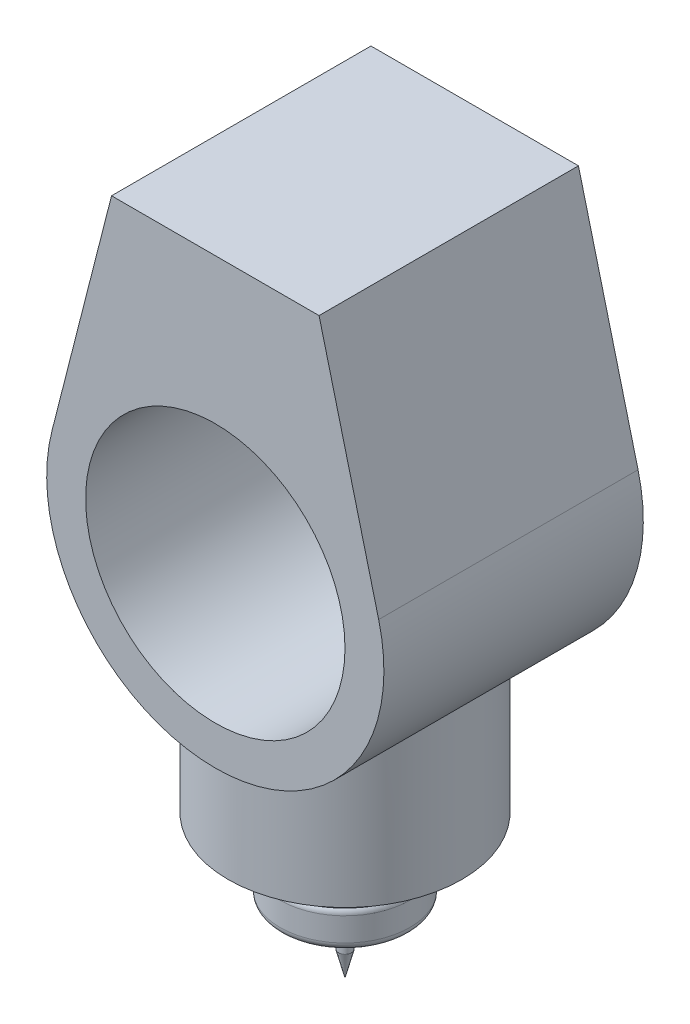
SolidWorks part; units mm, degrees
ref_plane "Front Plane" through (0, 0, 0) normal (0, 0, 1) x (1, 0, 0)
ref_plane "Top Plane" through (0, 0, 0) normal (0, 1, 0) x (1, 0, 0)
ref_plane "Right Plane" through (0, 0, 0) normal (1, 0, 0) x (0, 0, -1)
sketch "Sketch1" plane through (0, 0, 0) normal (0, 0, 1) x (1, 0, 0)
  line L0 (0, -45.712) -> (0, 32.0347) construction
  line L1 (0, 15.2605) -> (-20, 15.2605)
  line L2 (-20, 15.2605) -> (-20, 1.2605)
  line L3 (-20, 1.2605) -> (-25, 1.2605)
  line L4 (-25, 1.2605) -> (-25, -13.7395)
  line L5 (-25, -13.7395) -> (-10, -13.7395)
  line L6 (-10, -13.7395) -> (-5, -22.3997)
  line L7 (-5, -22.3997) -> (-2.5, -22.3997)
  line L8 (-2.5, -22.3997) -> (-2.5, -30.3997)
  line L9 (-2.5, -30.3997) -> (0, -40.0822)
  line L10 (0, 15.2605) -> (0, -40.0822)
  dimension "D1" = 20
  dimension "D2" = 14
  dimension "D3" = 5
  dimension "D4" = 15
  dimension "D5" = 15
  dimension "D6" = 120
  dimension "D7" = 10
  dimension "D8" = 10
  dimension "D9" = 2.5
  dimension "D10" = 8
revolve "Revolve1" add sketch "Sketch1" angle 360 about L0
fillet "Fillet1" radius 3 1 edges at (0, 1.2605, -20)
fillet "Fillet2" radius 3 2 edges at (0, -13.7395, -25) (0, 1.2605, -25)
sketch "Sketch2" plane through (0, 0, 0) normal (0, 0, 1) x (1, 0, 0)
  line L0 (40, 226.0804) -> (-40, 226.0804)
  line L1 (40, 226.0804) -> (62.9795, 136.0804)
  line L2 (-40, 226.0804) -> (-62.9795, 136.0804)
  arc A0 (-62.9795, 136.0804) -> (62.9795, 136.0804) centre (0, 120) ccw
  circle A1 centre (0, 120) radius 50
  point P6 (0, 226.0804)
  dimension "D1" = 120
  dimension "D2" = 130
  dimension "D6" = 100
  dimension "D3" = 80
  dimension "D4" = 90
  dimension "D5" = 90
extrude "Boss-Extrude1" add sketch "Sketch2" along normal mid plane 100 separate body
sketch "Sketch3" plane through (0, 15.2605, 0) normal (0, 1, 0) x (1, 0, 0)
  circle A0 centre (0, 0) radius 45
  dimension "D1" = 90
extrude "Boss-Extrude3" add sketch "Sketch3" along normal up to next
sketch "Sketch4" plane through (0, 15.2605, 0) normal (0, -1, 0) x (1, 0, 0)
  circle A0 centre (0, 0) radius 32.5
  dimension "D1" = 65
extrude "Boss-Extrude4" add sketch "Sketch4" along normal blind 10
fillet "Fillet3" radius 2 1 edges at (0, 15.2605, 32.5)
fillet "Fillet4" radius 2 1 edges at (0, 5.2605, -32.5)
sketch "Sketch5" plane through (0, 15.2605, 0) normal (0, -1, 0) x (1, 0, 0)
  circle A0 centre (0, 40) radius 4
  circle A1 centre (0, -40) radius 4
  circle A2 centre (0, 0) radius 45 construction
  dimension "D1" = 8
  dimension "D2" = 8
  dimension "D3" = 80
  dimension "D4" = 40
extrude "Cut-Extrude1" cut sketch "Sketch5" against normal blind 5 contours A0
pattern_circular "CirPattern1" count 6 over 360 about axis through (0, 0, 0) along (0, 1, 0) of "Cut-Extrude1"
sketch "Sketch6" plane through (0, 0, 0) normal (0, 0, 1) x (1, 0, 0)
  point P0 (0, 120)
ref_plane "Plane1" through (0, -40.0822, 0) normal (0, -1, 0) x (-1, 0, 0)
sketch "Sketch7" plane through (0, -40.0822, 0) normal (0, -1, 0) x (-1, 0, 0)
  point P0 (0, 0)
